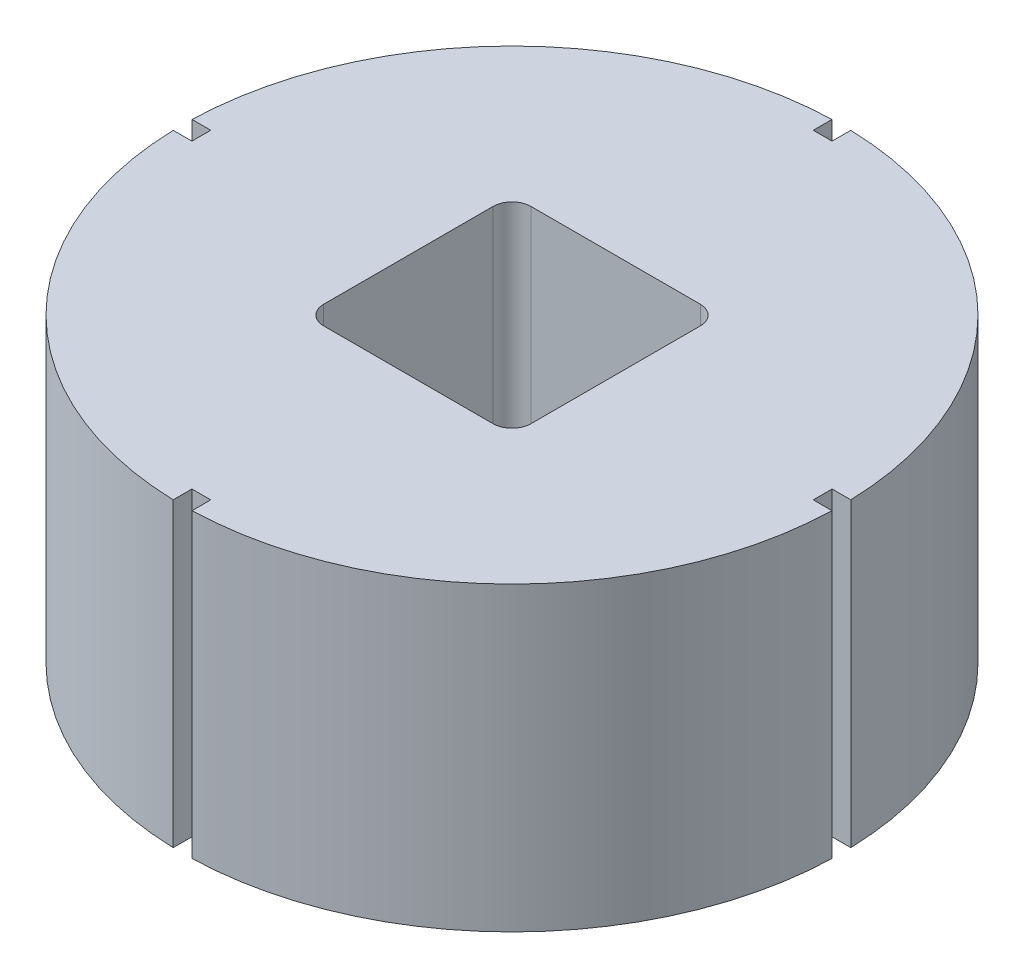
SolidWorks part; units mm, degrees
ref_plane "Front Plane" through (0, 0, 0) normal (0, 0, 1) x (1, 0, 0)
ref_plane "Top Plane" through (0, 0, 0) normal (0, 1, 0) x (1, 0, 0)
ref_plane "Right Plane" through (0, 0, 0) normal (1, 0, 0) x (0, 0, -1)
sketch "Sketch1" plane through (0, 0, 0) normal (0, 1, 0) x (1, 0, 0)
  circle A0 centre (0, 0) radius 35
  dimension "D1" = 70
extrude "Boss-Extrude1" add sketch "Sketch1" along normal blind 32
sketch "Sketch2" plane through (0, 0, 0) normal (0, -1, 0) x (1, 0, 0)
  circle A0 centre (0, 0) radius 10
  dimension "D1" = 20
extrude "Boss-Extrude2" add sketch "Sketch2" along normal blind 5
sketch "Sketch3" plane through (0, 32, 0) normal (0, 1, 0) x (1, 0, 0)
  line L1 (-9, 11) -> (9, 11)
  line L2 (-11, 9) -> (-11, -9)
  line L3 (-9, -11) -> (9, -11)
  line L4 (11, 9) -> (11, -9)
  line L5 (-11, 11) -> (11, -11) construction
  line L6 (-11, -11) -> (11, 11) construction
  arc A0 (-11, -9) -> (-9, -11) centre (-9, -9) ccw
  arc A1 (9, -11) -> (11, -9) centre (9, -9) ccw
  arc A2 (9, 11) -> (11, 9) centre (9, 9) cw
  arc A3 (-9, 11) -> (-11, 9) centre (-9, 9) ccw
  point P0 (0, 0)
  dimension "D3" = 2
  dimension "D1" = 22
  dimension "D2" = 22
extrude "Cut-Extrude1" cut sketch "Sketch3" against normal blind 25
sketch "Sketch4" plane through (0, 32, 0) normal (0, 1, 0) x (1, 0, 0)
  line L0 (0, 35) -> (0, -35) construction
  line L1 (-1, 34.9857) -> (-1, 33)
  line L2 (-1, 33) -> (1, 33)
  line L3 (1, 33) -> (1, 34.9857)
  line L4 (34.9857, 1) -> (33, 1)
  line L5 (33, 1) -> (33, -1)
  line L6 (33, -1) -> (34.9857, -1)
  line L7 (1, -34.9857) -> (1, -33)
  line L8 (1, -33) -> (-1, -33)
  line L9 (-1, -33) -> (-1, -34.9857)
  line L10 (-34.9857, -1) -> (-33, -1)
  line L11 (-33, -1) -> (-33, 1)
  line L12 (-33, 1) -> (-34.9857, 1)
  circle A0 centre (0, 0) radius 35 construction
  arc A1 (1, 34.9857) -> (-1, 34.9857) centre (0, 0) ccw
  arc A2 (34.9857, -1) -> (34.9857, 1) centre (0, 0) ccw
  arc A3 (-1, -34.9857) -> (1, -34.9857) centre (0, 0) ccw
  arc A4 (-34.9857, 1) -> (-34.9857, -1) centre (0, 0) ccw
  point P24 (0, 0)
  dimension "D1" = 1
  dimension "D2" = 1
  dimension "D3" = 2
  dimension "D4" = 4
extrude "Cut-Extrude2" cut sketch "Sketch4" against normal blind 36
